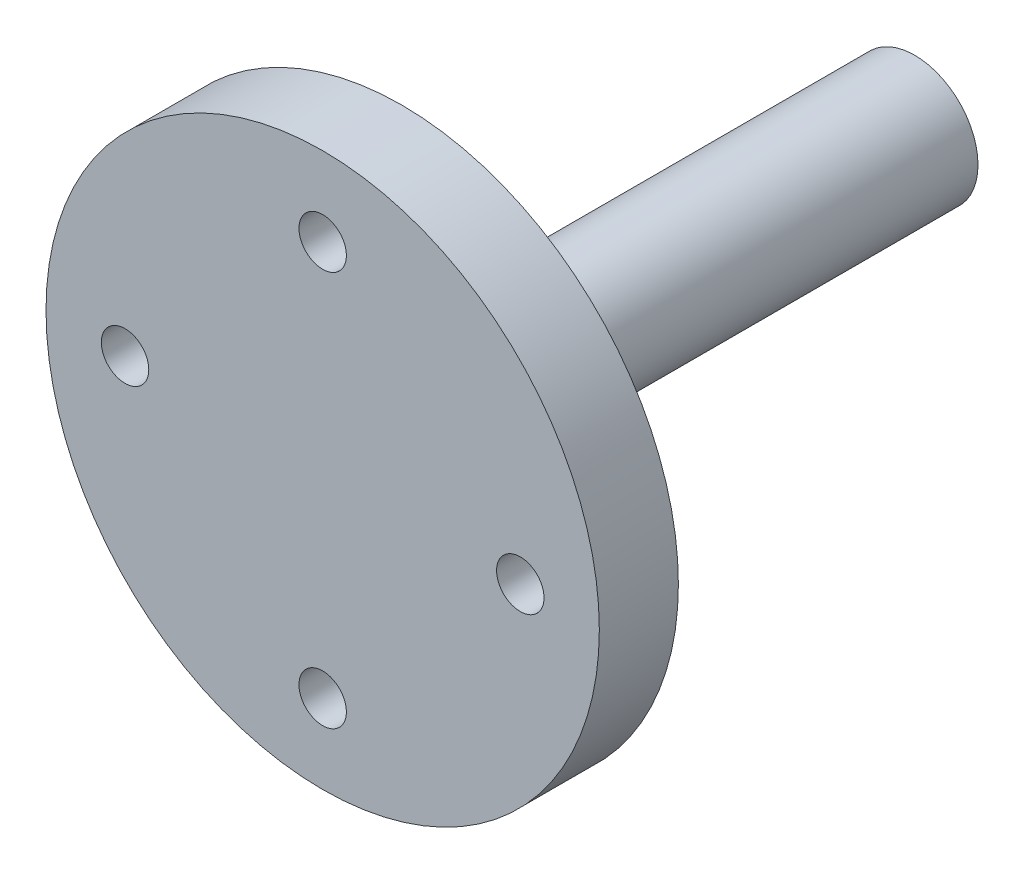
SolidWorks part; units mm, degrees
material "6061 Alloy"
ref_plane "Front Plane" through (0, 0, 0) normal (0, 0, 1) x (1, 0, 0)
ref_plane "Top Plane" through (0, 0, 0) normal (0, 1, 0) x (1, 0, 0)
ref_plane "Right Plane" through (0, 0, 0) normal (1, 0, 0) x (0, 0, -1)
sketch "Sketch1" plane through (0, 0, 0) normal (0, 0, 1) x (1, 0, 0)
  circle A0 centre (0, 0) radius 4
  dimension "D1" = 8
extrude "Boss-Extrude1" add sketch "Sketch1" against normal blind 20 and the other way blind 12.4511
sketch "Sketch3" plane through (0, 0, 12.4511) normal (0, 0, 1) x (1, 0, 0)
  circle A0 centre (0, 0) radius 17.5
  circle A1 centre (0, 0) radius 12.5 construction
  circle A2 centre (0, 12.5) radius 1.5
  circle A3 centre (12.5, 0) radius 1.5
  circle A4 centre (0, -12.5) radius 1.5
  circle A5 centre (-12.5, 0) radius 1.5
  point P15 (0, 0)
  dimension "D1" = 35
  dimension "D2" = 25
  dimension "D3" = 3
  dimension "D4" = 4
extrude "Boss-Extrude2" add sketch "Sketch3" along normal blind 5
fillet "Fillet1" radius 3 1 edges at (4, 0, 12.4511)
